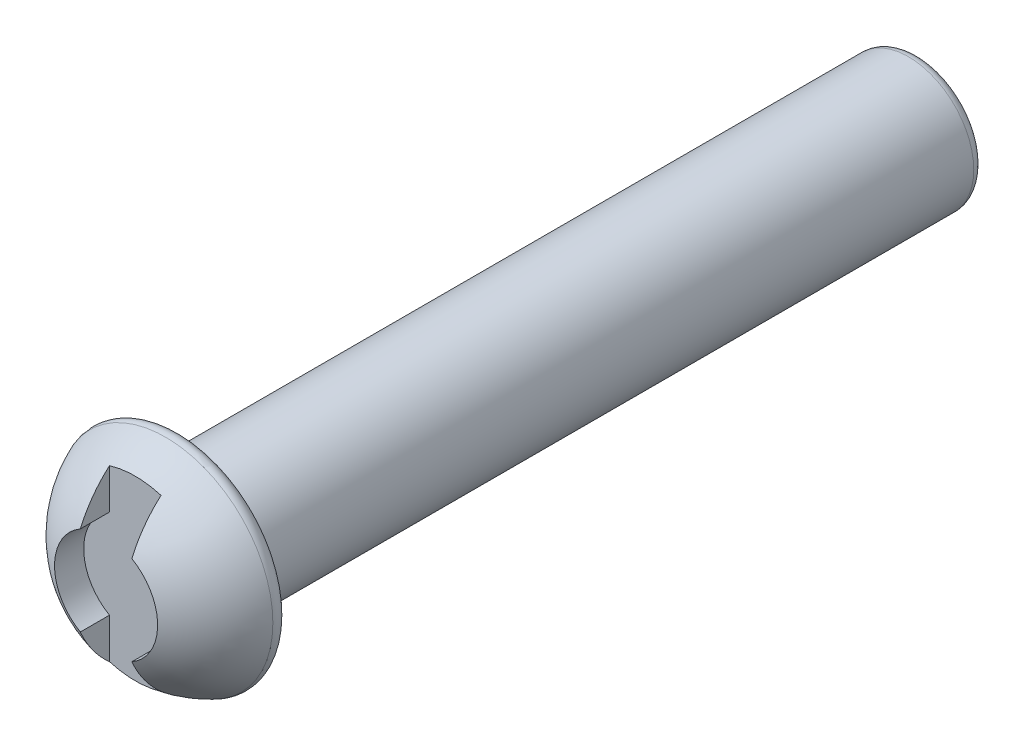
SolidWorks part; units mm, degrees
ref_plane "Front Plane" through (0, 0, 0) normal (0, 0, 1) x (1, 0, 0)
ref_plane "Top Plane" through (0, 0, 0) normal (0, 1, 0) x (1, 0, 0)
ref_plane "Right Plane" through (0, 0, 0) normal (1, 0, 0) x (0, 0, -1)
sketch "Sketch1" plane through (0, 0, 0) normal (1, 0, 0) x (0, 0, -1)
  line L0 (0, 0) -> (60, 0)
  line L1 (60, 0) -> (60, 4.75)
  line L2 (60, 4.75) -> (6.25, 4.75)
  line L3 (6.25, 4.75) -> (6.25, 8.15)
  arc A0 (6.25, 8.15) -> (0, 0) centre (8.4388, 0) ccw
  point P7 (0, 0)
  dimension "D1" = 4.75
  dimension "D2" = 60
  dimension "D3" = 8.15
  dimension "D4" = 6.25
revolve "Revolve1" add sketch "Sketch1" angle 360 about L0
ref_plane "Plane1" through (0, 0, 0) normal (0, 0, 1) x (1, 0, 0)
sketch "Sketch2" plane through (0, 0, 0) normal (0, 0, 1) x (1, 0, 0)
  line L0 (-1.875, 3.2476) -> (-1.875, 12.5581)
  line L1 (-1.875, -12.5581) -> (1.875, -12.5581)
  line L2 (-1.875, -12.5581) -> (-1.875, -3.2476)
  line L3 (-1.875, 12.5581) -> (1.875, 12.5581)
  line L4 (1.875, -12.5581) -> (1.875, -3.2476)
  line L5 (-1.875, -12.5581) -> (1.875, 12.5581) construction
  line L6 (-1.875, 12.5581) -> (1.875, -12.5581) construction
  line L7 (1.875, 3.2476) -> (1.875, 12.5581)
  arc A1 (-1.875, 3.2476) -> (-1.875, -3.2476) centre (0, 0) ccw
  arc A3 (1.875, -3.2476) -> (1.875, 3.2476) centre (0, 0) ccw
  point P0 (0, 0)
  dimension "D1" = 3.75
fillet "Fillet1" radius 0.75 2 edges at (4.75, 0, -60) (8.15, 0, -6.25)
sketch "Sketch3" plane through (0, 0, 0) normal (0, 0, 1) x (1, 0, 0)
  line L0 (1.875, -3.2476) -> (1.875, -8.653)
  line L1 (-1.875, 8.653) -> (1.875, 8.653)
  line L2 (-1.875, 8.653) -> (-1.875, 3.2476)
  line L3 (-1.875, -8.653) -> (1.875, -8.653)
  line L4 (1.875, 8.653) -> (1.875, 3.2476)
  line L5 (-1.875, 8.653) -> (1.875, -8.653) construction
  line L6 (-1.875, -8.653) -> (1.875, 8.653) construction
  line L7 (-1.875, -3.2476) -> (-1.875, -8.653)
  arc A0 (-1.875, 3.2476) -> (-1.875, -3.2476) centre (0, 0) ccw
  arc A1 (1.875, -3.2476) -> (1.875, 3.2476) centre (0, 0) ccw
  point P0 (0, 0)
  dimension "D1" = 7.5
  dimension "D2" = 3.75
extrude "Cut-Extrude2" cut sketch "Sketch3" against normal blind 3
